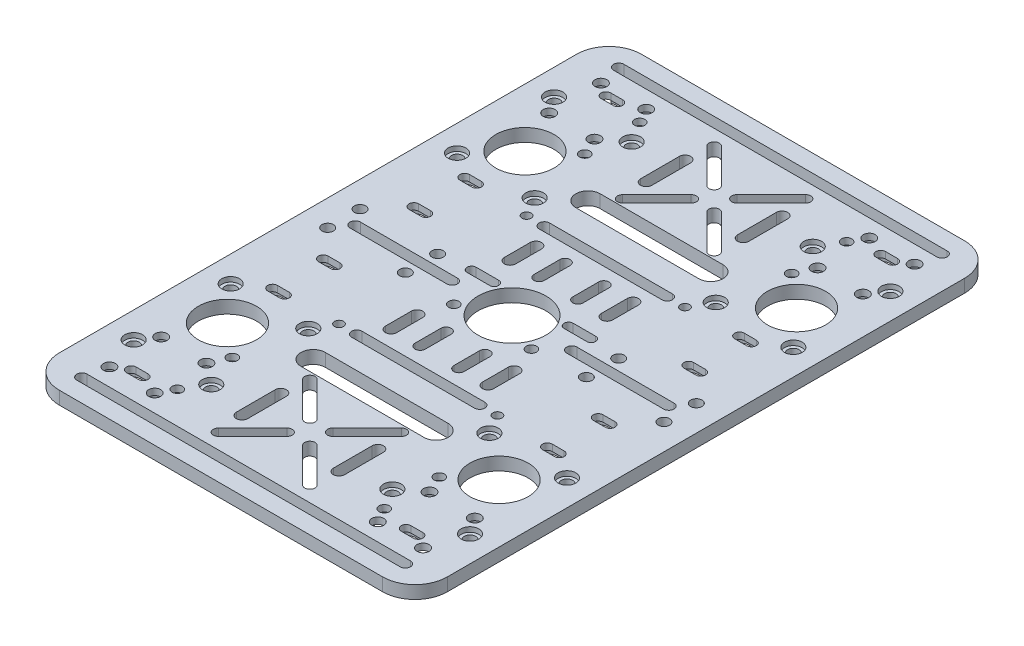
SolidWorks part; units mm, degrees
ref_plane "Front Plane" through (0, 0, 0) normal (0, 0, 1) x (1, 0, 0)
ref_plane "Top Plane" through (0, 0, 0) normal (0, 1, 0) x (1, 0, 0)
ref_plane "Right Plane" through (0, 0, 0) normal (1, 0, 0) x (0, 0, -1)
sketch "Sketch1" plane through (0, 0, 0) normal (0, 1, 0) x (1, 0, 0)
  line L0 (0, 172.909) -> (0, -52.3008) construction
  line L1 (-60, -90) -> (60, -90)
  line L2 (-60, -90) -> (-60, 90)
  line L3 (-60, 90) -> (60, 90)
  line L4 (60, -90) -> (60, 90)
  line L5 (-60, -90) -> (60, 90) construction
  line L6 (-60, 90) -> (60, -90) construction
  line L7 (0, 0) -> (91.3334, 0) construction
  line L8 (-34.5, 171.6818) -> (-34.5, -164.6355) construction
  line L9 (-48.5, 31.1899) -> (-48.5, -305.1274) construction
  line L10 (-15, 68.5) -> (-15, 56.5) construction
  line L13 (-16.75, 68.5) -> (-16.75, 56.5)
  line L16 (-13.25, 68.5) -> (-13.25, 56.5)
  line L19 (15, -68.5) -> (15, -56.5) construction
  line L22 (16.75, -68.5) -> (16.75, -56.5)
  line L25 (13.25, -68.5) -> (13.25, -56.5)
  line L28 (-15, -68.5) -> (-15, -56.5) construction
  line L31 (-16.75, -68.5) -> (-16.75, -56.5)
  line L34 (11.5, 6) -> (18.5, 6) construction
  line L35 (-24.5, -29) -> (24.5, -29) construction
  line L36 (-24.5, -29) -> (-24.5, 29) construction
  line L37 (-24.5, 29) -> (24.5, 29) construction
  line L38 (24.5, -29) -> (24.5, 29) construction
  line L39 (-24.5, -29) -> (24.5, 29) construction
  line L40 (-24.5, 29) -> (24.5, -29) construction
  line L41 (11.5, 7.4) -> (18.5, 7.4)
  line L42 (11.5, 4.6) -> (18.5, 4.6)
  line L43 (-11.5, 6) -> (-18.5, 6) construction
  line L44 (-11.5, 7.4) -> (-18.5, 7.4)
  line L45 (-11.5, 4.6) -> (-18.5, 4.6)
  line L46 (3.5355, 58.9645) -> (14.1421, 48.3579) construction
  line L47 (-17.5, 80) -> (17.5, 80) construction
  line L48 (-17.5, 80) -> (-17.5, 45) construction
  line L49 (-17.5, 45) -> (17.5, 45) construction
  line L50 (17.5, 80) -> (17.5, 45) construction
  line L51 (-17.5, 80) -> (17.5, 45) construction
  line L52 (-17.5, 45) -> (17.5, 80) construction
  line L53 (4.6669, 60.0958) -> (15.2735, 49.4892)
  line L54 (2.4042, 57.8331) -> (13.0108, 47.2265)
  line L55 (-3.5355, 58.9645) -> (-14.1421, 48.3579) construction
  line L56 (-2.4042, 57.8331) -> (-13.0108, 47.2265)
  line L57 (-4.6669, 60.0958) -> (-15.2735, 49.4892)
  line L58 (-3.5355, 66.0355) -> (-14.1421, 76.6421) construction
  line L59 (-4.6669, 64.9042) -> (-15.2735, 75.5108)
  line L60 (-2.4042, 67.1669) -> (-13.0108, 77.7735)
  line L61 (3.5355, 66.0355) -> (14.1421, 76.6421) construction
  line L62 (2.4042, 67.1669) -> (13.0108, 77.7735)
  line L63 (4.6669, 64.9042) -> (15.2735, 75.5108)
  line L64 (3.5355, -58.9645) -> (14.1421, -48.3579) construction
  line L65 (4.6669, -60.0958) -> (15.2735, -49.4892)
  line L66 (2.4042, -57.8331) -> (13.0108, -47.2265)
  line L67 (-3.5355, -58.9645) -> (-14.1421, -48.3579) construction
  line L68 (-2.4042, -57.8331) -> (-13.0108, -47.2265)
  line L69 (-4.6669, -60.0958) -> (-15.2735, -49.4892)
  line L70 (-3.5355, -66.0355) -> (-14.1421, -76.6421) construction
  line L71 (-4.6669, -64.9042) -> (-15.2735, -75.5108)
  line L72 (-2.4042, -67.1669) -> (-13.0108, -77.7735)
  line L73 (3.5355, -66.0355) -> (14.1421, -76.6421) construction
  line L74 (2.4042, -67.1669) -> (13.0108, -77.7735)
  line L75 (4.6669, -64.9042) -> (15.2735, -75.5108)
  line L76 (-19, -42.5) -> (19, -42.5) construction
  line L77 (-29.7, -42.5) -> (29.7, -42.5) construction
  line L79 (-29.7, 42.5) -> (29.7, 42.5) construction
  line L83 (-19, -38.75) -> (19, -38.75)
  line L84 (-19, -46.25) -> (19, -46.25)
  line L85 (-19, 42.5) -> (19, 42.5) construction
  line L86 (-19, 38.75) -> (19, 38.75)
  line L87 (-19, 46.25) -> (19, 46.25)
  line L88 (-48.5, 0) -> (-18.5, 0) construction
  line L97 (-48.5, 1.6) -> (-18.5, 1.6)
  line L98 (-48.5, -1.6) -> (-18.5, -1.6)
  line L99 (-50, -83) -> (50, -83) construction
  line L100 (-50, -81.4) -> (50, -81.4)
  line L101 (-50, -84.6) -> (50, -84.6)
  line L102 (48.5, 0) -> (18.5, 0) construction
  line L103 (48.5, 1.6) -> (18.5, 1.6)
  line L104 (48.5, -1.6) -> (18.5, -1.6)
  line L105 (-50, 83) -> (50, 83) construction
  line L106 (-50, 81.4) -> (50, 81.4)
  line L107 (-50, 84.6) -> (50, 84.6)
  line L108 (15, 68.5) -> (15, 56.5) construction
  line L109 (16.75, 68.5) -> (16.75, 56.5)
  line L110 (13.25, 68.5) -> (13.25, 56.5)
  line L111 (-13.25, -68.5) -> (-13.25, -56.5)
  line L114 (40.65, -29.7) -> (44.35, -29.7) construction
  line L120 (-19, 29) -> (19, 29) construction
  line L121 (-19, 30.6) -> (19, 30.6)
  line L122 (-19, 27.4) -> (19, 27.4)
  line L123 (-6, 22.4) -> (-6, 14.4) construction
  line L124 (-4.4, 22.4) -> (-4.4, 14.4)
  line L125 (-7.6, 22.4) -> (-7.6, 14.4)
  line L126 (-15, 22.4) -> (-15, 14.4) construction
  line L127 (-13.25, 22.4) -> (-13.25, 14.4)
  line L128 (-16.75, 22.4) -> (-16.75, 14.4)
  line L129 (15, 22.4) -> (15, 14.4) construction
  line L130 (13.25, 22.4) -> (13.25, 14.4)
  line L131 (16.75, 22.4) -> (16.75, 14.4)
  line L132 (6, 22.4) -> (6, 14.4) construction
  line L133 (4.4, 22.4) -> (4.4, 14.4)
  line L134 (7.6, 22.4) -> (7.6, 14.4)
  line L135 (15, -22.4) -> (15, -14.4) construction
  line L136 (13.25, -22.4) -> (13.25, -14.4)
  line L137 (16.75, -22.4) -> (16.75, -14.4)
  line L138 (6, -22.4) -> (6, -14.4) construction
  line L139 (4.4, -22.4) -> (4.4, -14.4)
  line L140 (7.6, -22.4) -> (7.6, -14.4)
  line L141 (-6, -22.4) -> (-6, -14.4) construction
  line L142 (-4.4, -22.4) -> (-4.4, -14.4)
  line L143 (-7.6, -22.4) -> (-7.6, -14.4)
  line L144 (-15, -22.4) -> (-15, -14.4) construction
  line L145 (-13.25, -22.4) -> (-13.25, -14.4)
  line L146 (-16.75, -22.4) -> (-16.75, -14.4)
  line L147 (-19, -29) -> (19, -29) construction
  line L148 (-19, -30.6) -> (19, -30.6)
  line L149 (-19, -27.4) -> (19, -27.4)
  line L150 (-42.5, 29.7) -> (42.5, 29.7) construction
  line L151 (-42.5, 29.7) -> (-42.5, -29.7) construction
  line L152 (-42.5, -29.7) -> (42.5, -29.7) construction
  line L153 (42.5, 29.7) -> (42.5, -29.7) construction
  line L154 (-42.5, 29.7) -> (42.5, -29.7) construction
  line L155 (-42.5, -29.7) -> (42.5, 29.7) construction
  line L156 (40.65, -28.2) -> (44.35, -28.2)
  line L157 (40.65, -31.2) -> (44.35, -31.2)
  line L158 (40.65, 29.7) -> (44.35, 29.7) construction
  line L159 (40.65, 28.2) -> (44.35, 28.2)
  line L160 (40.65, 31.2) -> (44.35, 31.2)
  line L161 (-40.65, -29.7) -> (-44.35, -29.7) construction
  line L162 (-40.65, -28.2) -> (-44.35, -28.2)
  line L163 (-40.65, -31.2) -> (-44.35, -31.2)
  line L164 (-40.65, 29.7) -> (-44.35, 29.7) construction
  line L165 (-40.65, 28.2) -> (-44.35, 28.2)
  line L166 (-40.65, 31.2) -> (-44.35, 31.2)
  line L167 (44.35, -14) -> (40.65, -14) construction
  line L168 (44.35, -15.5) -> (40.65, -15.5)
  line L169 (44.35, -12.5) -> (40.65, -12.5)
  line L170 (88.9718, -43.7) -> (45.9541, -43.7) construction
  line L173 (-44.35, -14) -> (-40.65, -14) construction
  line L176 (-44.35, -15.5) -> (-40.65, -15.5)
  line L179 (-44.35, -12.5) -> (-40.65, -12.5)
  line L180 (-44.35, -73.4) -> (-40.65, -73.4) construction
  line L181 (-44.35, -71.9) -> (-40.65, -71.9)
  line L182 (-44.35, -74.9) -> (-40.65, -74.9)
  line L183 (44.35, -73.4) -> (40.65, -73.4) construction
  line L184 (44.35, -71.9) -> (40.65, -71.9)
  line L185 (44.35, -74.9) -> (40.65, -74.9)
  line L186 (44.35, 73.4) -> (40.65, 73.4) construction
  line L187 (44.35, 71.9) -> (40.65, 71.9)
  line L188 (44.35, 74.9) -> (40.65, 74.9)
  line L189 (-44.35, 73.4) -> (-40.65, 73.4) construction
  line L190 (-44.35, 71.9) -> (-40.65, 71.9)
  line L191 (-44.35, 74.9) -> (-40.65, 74.9)
  line L192 (44.35, 14) -> (40.65, 14) construction
  line L193 (44.35, 15.5) -> (40.65, 15.5)
  line L194 (44.35, 12.5) -> (40.65, 12.5)
  line L195 (-44.35, 14) -> (-40.65, 14) construction
  line L196 (-44.35, 15.5) -> (-40.65, 15.5)
  line L197 (-44.35, 12.5) -> (-40.65, 12.5)
  circle A16 centre (-24.5, 29) radius 1.4
  circle A17 centre (24.5, 29) radius 1.4
  circle A18 centre (-24.5, -29) radius 1.4
  circle A19 centre (24.5, -29) radius 1.4
  arc A20 (11.5, 7.4) -> (11.5, 4.6) centre (11.5, 6) ccw
  arc A21 (18.5, 4.6) -> (18.5, 7.4) centre (18.5, 6) ccw
  arc A22 (-11.5, 7.4) -> (-11.5, 4.6) centre (-11.5, 6) cw
  arc A23 (-18.5, 4.6) -> (-18.5, 7.4) centre (-18.5, 6) cw
  circle A24 centre (0, 0) radius 10.5
  arc A25 (4.6669, 60.0958) -> (2.4042, 57.8331) centre (3.5355, 58.9645) ccw
  arc A26 (13.0108, 47.2265) -> (15.2735, 49.4892) centre (14.1421, 48.3579) ccw
  arc A28 (-2.4042, 57.8331) -> (-4.6669, 60.0958) centre (-3.5355, 58.9645) ccw
  arc A29 (-15.2735, 49.4892) -> (-13.0108, 47.2265) centre (-14.1421, 48.3579) ccw
  arc A30 (-4.6669, 64.9042) -> (-2.4042, 67.1669) centre (-3.5355, 66.0355) ccw
  arc A31 (-13.0108, 77.7735) -> (-15.2735, 75.5108) centre (-14.1421, 76.6421) ccw
  arc A32 (2.4042, 67.1669) -> (4.6669, 64.9042) centre (3.5355, 66.0355) ccw
  arc A33 (15.2735, 75.5108) -> (13.0108, 77.7735) centre (14.1421, 76.6421) ccw
  arc A34 (4.6669, -60.0958) -> (2.4042, -57.8331) centre (3.5355, -58.9645) cw
  arc A35 (13.0108, -47.2265) -> (15.2735, -49.4892) centre (14.1421, -48.3579) cw
  arc A36 (-2.4042, -57.8331) -> (-4.6669, -60.0958) centre (-3.5355, -58.9645) cw
  arc A37 (-15.2735, -49.4892) -> (-13.0108, -47.2265) centre (-14.1421, -48.3579) cw
  arc A38 (-4.6669, -64.9042) -> (-2.4042, -67.1669) centre (-3.5355, -66.0355) cw
  arc A39 (-13.0108, -77.7735) -> (-15.2735, -75.5108) centre (-14.1421, -76.6421) cw
  arc A40 (2.4042, -67.1669) -> (4.6669, -64.9042) centre (3.5355, -66.0355) cw
  arc A41 (15.2735, -75.5108) -> (13.0108, -77.7735) centre (14.1421, -76.6421) cw
  circle A42 centre (12, -6) radius 1.6
  circle A43 centre (-12, -6) radius 1.6
  arc A48 (-19, -38.75) -> (-19, -46.25) centre (-19, -42.5) ccw
  arc A49 (19, -46.25) -> (19, -38.75) centre (19, -42.5) ccw
  arc A50 (-19, 38.75) -> (-19, 46.25) centre (-19, 42.5) cw
  arc A51 (19, 46.25) -> (19, 38.75) centre (19, 42.5) cw
  arc A52 (-48.5, 1.6) -> (-48.5, -1.6) centre (-48.5, 0) ccw
  arc A53 (-18.5, -1.6) -> (-18.5, 1.6) centre (-18.5, 0) ccw
  arc A54 (-50, -81.4) -> (-50, -84.6) centre (-50, -83) ccw
  arc A55 (50, -84.6) -> (50, -81.4) centre (50, -83) ccw
  arc A56 (48.5, 1.6) -> (48.5, -1.6) centre (48.5, 0) cw
  arc A57 (18.5, -1.6) -> (18.5, 1.6) centre (18.5, 0) cw
  arc A58 (-50, 81.4) -> (-50, 84.6) centre (-50, 83) cw
  arc A59 (50, 84.6) -> (50, 81.4) centre (50, 83) cw
  arc A60 (16.75, 68.5) -> (13.25, 68.5) centre (15, 68.5) ccw
  arc A61 (13.25, 56.5) -> (16.75, 56.5) centre (15, 56.5) ccw
  arc A68 (-19, 30.6) -> (-19, 27.4) centre (-19, 29) ccw
  arc A69 (19, 27.4) -> (19, 30.6) centre (19, 29) ccw
  arc A70 (-4.4, 22.4) -> (-7.6, 22.4) centre (-6, 22.4) ccw
  arc A71 (-7.6, 14.4) -> (-4.4, 14.4) centre (-6, 14.4) ccw
  arc A72 (-13.25, 22.4) -> (-16.75, 22.4) centre (-15, 22.4) ccw
  arc A73 (-16.75, 14.4) -> (-13.25, 14.4) centre (-15, 14.4) ccw
  arc A74 (13.25, 22.4) -> (16.75, 22.4) centre (15, 22.4) cw
  arc A75 (16.75, 14.4) -> (13.25, 14.4) centre (15, 14.4) cw
  arc A76 (4.4, 22.4) -> (7.6, 22.4) centre (6, 22.4) cw
  arc A77 (7.6, 14.4) -> (4.4, 14.4) centre (6, 14.4) cw
  arc A78 (13.25, -22.4) -> (16.75, -22.4) centre (15, -22.4) ccw
  arc A79 (16.75, -14.4) -> (13.25, -14.4) centre (15, -14.4) ccw
  arc A80 (4.4, -22.4) -> (7.6, -22.4) centre (6, -22.4) ccw
  arc A81 (7.6, -14.4) -> (4.4, -14.4) centre (6, -14.4) ccw
  arc A82 (-4.4, -22.4) -> (-7.6, -22.4) centre (-6, -22.4) cw
  arc A83 (-7.6, -14.4) -> (-4.4, -14.4) centre (-6, -14.4) cw
  arc A84 (-13.25, -22.4) -> (-16.75, -22.4) centre (-15, -22.4) cw
  arc A85 (-16.75, -14.4) -> (-13.25, -14.4) centre (-15, -14.4) cw
  arc A86 (-19, -30.6) -> (-19, -27.4) centre (-19, -29) cw
  arc A87 (19, -27.4) -> (19, -30.6) centre (19, -29) cw
  arc A96 (-16.75, 68.5) -> (-13.25, 68.5) centre (-15, 68.5) cw
  arc A97 (-13.25, 56.5) -> (-16.75, 56.5) centre (-15, 56.5) cw
  arc A98 (16.75, -68.5) -> (13.25, -68.5) centre (15, -68.5) cw
  arc A99 (13.25, -56.5) -> (16.75, -56.5) centre (15, -56.5) cw
  arc A100 (-16.75, -68.5) -> (-13.25, -68.5) centre (-15, -68.5) ccw
  arc A101 (-13.25, -56.5) -> (-16.75, -56.5) centre (-15, -56.5) ccw
  arc A102 (40.65, -28.2) -> (40.65, -31.2) centre (40.65, -29.7) ccw
  arc A103 (44.35, -31.2) -> (44.35, -28.2) centre (44.35, -29.7) ccw
  arc A104 (40.65, 28.2) -> (40.65, 31.2) centre (40.65, 29.7) cw
  arc A105 (44.35, 31.2) -> (44.35, 28.2) centre (44.35, 29.7) cw
  arc A106 (-40.65, -28.2) -> (-40.65, -31.2) centre (-40.65, -29.7) cw
  arc A107 (-44.35, -31.2) -> (-44.35, -28.2) centre (-44.35, -29.7) cw
  arc A108 (-40.65, 28.2) -> (-40.65, 31.2) centre (-40.65, 29.7) ccw
  arc A109 (-44.35, 31.2) -> (-44.35, 28.2) centre (-44.35, 29.7) ccw
  arc A110 (44.35, -15.5) -> (44.35, -12.5) centre (44.35, -14) ccw
  arc A111 (40.65, -12.5) -> (40.65, -15.5) centre (40.65, -14) ccw
  arc A118 (-44.35, -15.5) -> (-44.35, -12.5) centre (-44.35, -14) cw
  arc A119 (-40.65, -12.5) -> (-40.65, -15.5) centre (-40.65, -14) cw
  arc A120 (-44.35, -71.9) -> (-44.35, -74.9) centre (-44.35, -73.4) ccw
  arc A121 (-40.65, -74.9) -> (-40.65, -71.9) centre (-40.65, -73.4) ccw
  arc A122 (44.35, -71.9) -> (44.35, -74.9) centre (44.35, -73.4) cw
  arc A123 (40.65, -74.9) -> (40.65, -71.9) centre (40.65, -73.4) cw
  arc A124 (44.35, 71.9) -> (44.35, 74.9) centre (44.35, 73.4) ccw
  arc A125 (40.65, 74.9) -> (40.65, 71.9) centre (40.65, 73.4) ccw
  arc A126 (-44.35, 71.9) -> (-44.35, 74.9) centre (-44.35, 73.4) cw
  arc A127 (-40.65, 74.9) -> (-40.65, 71.9) centre (-40.65, 73.4) cw
  arc A128 (44.35, 15.5) -> (44.35, 12.5) centre (44.35, 14) cw
  arc A129 (40.65, 12.5) -> (40.65, 15.5) centre (40.65, 14) cw
  arc A130 (-44.35, 15.5) -> (-44.35, 12.5) centre (-44.35, 14) ccw
  arc A131 (-40.65, 12.5) -> (-40.65, 15.5) centre (-40.65, 14) ccw
  point P0 (0, 0)
  point P16 (-15, 62.5)
  point P23 (15, -62.5)
  point P30 (-15, -62.5)
  point P40 (42.5, -29.7)
  point P50 (42.5, -14)
  point P53 (42.5, 29.7)
  point P60 (-42.5, -29.7)
  point P67 (-42.5, 29.7)
  point P70 (0, 0)
  point P81 (15, 6)
  point P88 (-15, 6)
  point P95 (0, 62.5)
  point P100 (8.8388, 53.6612)
  point P110 (-8.8388, 53.6612)
  point P117 (-8.8388, 71.3388)
  point P124 (8.8388, 71.3388)
  point P131 (0, 62.5)
  point P134 (8.8388, -53.6612)
  point P141 (-8.8388, -53.6612)
  point P148 (-8.8388, -71.3388)
  point P155 (8.8388, -71.3388)
  point P171 (0, -42.5)
  point P179 (0, 42.5)
  point P185 (-33.5, 0)
  point P192 (0, -83)
  point P200 (33.5, 0)
  point P207 (0, 83)
  point P213 (15, 62.5)
  point P223 (-42.5, -14)
  point P230 (-42.5, -73.4)
  point P237 (42.5, -73.4)
  point P241 (0, 29)
  point P246 (-6, 18.4)
  point P253 (-15, 18.4)
  point P263 (15, 18.4)
  point P270 (6, 18.4)
  point P277 (15, -18.4)
  point P284 (6, -18.4)
  point P291 (-6, -18.4)
  point P298 (-15, -18.4)
  point P305 (0, -29)
  point P313 (42.5, 73.4)
  point P320 (-42.5, 73.4)
  point P327 (42.5, 14)
  point P334 (-42.5, 14)
  dimension "D11" = 2.8
  dimension "D15" = 21
  dimension "D21" = 15
  dimension "D24" = 3.2
  dimension "D29" = 3
  dimension "D32" = 3.2
  dimension "D39" = 3.2
  dimension "D50" = 14
  dimension "D1" = 120
  dimension "D2" = 180
  dimension "D3" = 14
  dimension "D5" = 34.5
  dimension "D6" = 30
  dimension "D7" = 42.5
  dimension "D8" = 42.5
  dimension "D9" = 49
  dimension "D10" = 58
  dimension "D12" = 7
  dimension "D13" = 2.8
  dimension "D14" = 30
  dimension "D16" = 6
  dimension "D17" = 35
  dimension "D18" = 35
  dimension "D19" = 10
  dimension "D20" = 3.2
  dimension "D22" = 5
  dimension "D25" = 24
  dimension "D26" = 6
  dimension "D27" = 85
  dimension "D28" = 59.4
  dimension "D30" = 38
  dimension "D31" = 7.5
  dimension "D33" = 3.2
  dimension "D34" = 100
  dimension "D35" = 83
  dimension "D36" = 30
  dimension "D37" = 3.5
  dimension "D38" = 12
  dimension "D40" = 38
  dimension "D41" = 8
  dimension "D42" = 3.2
  dimension "D43" = 6
  dimension "D44" = 5
  dimension "D45" = 9
  dimension "D46" = 3.5
  dimension "D47" = 3.7
  dimension "D48" = 3
  dimension "D49" = 3.7
  dimension "D51" = 29.7
  dimension "D23" = 4
extrude "Boss-Extrude1" add sketch "Sketch1" along normal blind 4
sketch "Sketch2" plane through (0, 4, 0) normal (0, 1, 0) x (1, 0, 0)
  line L0 (0, 0) -> (-78.829, 0) construction
  line L1 (-32, -71.5) -> (32, -71.5) construction
  line L2 (-32, -71.5) -> (-32, -54.5) construction
  line L3 (-32, -54.5) -> (32, -54.5) construction
  line L4 (32, -71.5) -> (32, -54.5) construction
  line L5 (-32, -71.5) -> (32, -54.5) construction
  line L6 (-32, -54.5) -> (32, -71.5) construction
  line L7 (0, 0) -> (0, 51.4904) construction
  line L12 (28, 65) -> (52, 65) construction
  line L13 (28, 65) -> (28, 35) construction
  line L14 (28, 35) -> (52, 35) construction
  line L15 (52, 65) -> (52, 35) construction
  line L16 (40, 65) -> (40, 35) construction
  line L17 (52, 50) -> (28, 50) construction
  line L19 (-48.5, 76) -> (-34.5, 76) construction
  line L20 (-48.5, 76) -> (-48.5, 60) construction
  line L21 (-48.5, 60) -> (-34.5, 60) construction
  line L22 (-34.5, 76) -> (-34.5, 60) construction
  line L23 (-48.5, 76) -> (-34.5, 60) construction
  line L24 (-48.5, 60) -> (-34.5, 76) construction
  circle A0 centre (32, -71.5) radius 1.6
  circle A1 centre (32, -54.5) radius 1.6
  circle A2 centre (-32, -71.5) radius 1.6
  circle A3 centre (-32, -54.5) radius 1.6
  circle A4 centre (32, 71.5) radius 1.6
  circle A5 centre (32, 54.5) radius 1.6
  circle A6 centre (-32, 71.5) radius 1.6
  circle A7 centre (-32, 54.5) radius 1.6
  circle A8 centre (52, 35) radius 1.75
  circle A9 centre (28, 35) radius 1.75
  circle A10 centre (28, 65) radius 1.75
  circle A11 centre (52, 65) radius 1.75
  circle A12 centre (-52, 65) radius 1.75
  circle A13 centre (-28, 65) radius 1.75
  circle A14 centre (-28, 35) radius 1.75
  circle A15 centre (-52, 35) radius 1.75
  circle A16 centre (-28, -65) radius 1.75
  circle A17 centre (-52, -65) radius 1.75
  circle A18 centre (-52, -35) radius 1.75
  circle A19 centre (-28, -35) radius 1.75
  circle A20 centre (52, -35) radius 1.75
  circle A21 centre (52, -65) radius 1.75
  circle A22 centre (28, -65) radius 1.75
  circle A23 centre (28, -35) radius 1.75
  circle A24 centre (28, 5) radius 1.75
  circle A25 centre (52, 5) radius 1.75
  circle A26 centre (28, -5) radius 1.75
  circle A27 centre (52, -5) radius 1.75
  circle A28 centre (-52, 5) radius 1.75
  circle A29 centre (-28, 5) radius 1.75
  circle A30 centre (-28, -5) radius 1.75
  circle A31 centre (-52, -5) radius 1.75
  circle A32 centre (-34.5, 76) radius 1.85
  circle A34 centre (-48.5, 76) radius 1.85
  circle A35 centre (-48.5, 60) radius 1.85
  circle A36 centre (-34.5, 60) radius 1.85
  circle A37 centre (34.5, 76) radius 1.85
  circle A38 centre (48.5, 76) radius 1.85
  circle A39 centre (48.5, 60) radius 1.85
  circle A40 centre (34.5, 60) radius 1.85
  circle A41 centre (-34.5, -76) radius 1.85
  circle A42 centre (-48.5, -76) radius 1.85
  circle A43 centre (-48.5, -60) radius 1.85
  circle A44 centre (-34.5, -60) radius 1.85
  circle A45 centre (34.5, -76) radius 1.85
  circle A46 centre (34.5, -60) radius 1.85
  circle A47 centre (48.5, -60) radius 1.85
  circle A48 centre (48.5, -76) radius 1.85
  point P0 (0, -63)
  point P20 (0, -63)
  point P35 (40, 50)
  point P76 (-41.5, 68)
  point P79 (0, 0)
  dimension "D4" = 3.2
  dimension "D5" = 3.2
  dimension "D6" = 3.2
  dimension "D7" = 3.2
  dimension "D10" = 3.5
  dimension "D15" = 3.7
  dimension "D16" = 2
  dimension "D1" = 63
  dimension "D2" = 64
  dimension "D3" = 17
  dimension "D8" = 24
  dimension "D9" = 30
  dimension "D11" = 40
  dimension "D12" = 50
  dimension "D13" = 14
  dimension "D14" = 16
  dimension "D18" = 34.5
  dimension "D19" = 60
  dimension "D17" = 2
extrude "Cut-Extrude1" cut sketch "Sketch2" against normal through all
fillet "Fillet1" radius 10 4 edges at (-60, 2, 90) (60, 2, 90) (60, 2, -90) (-60, 2, -90)
sketch "草图1" plane through (0, 4, 0) normal (0, 1, 0) x (1, 0, 0)
  line L0 (0, 0) -> (94.0983, 0) construction
  line L1 (0, 0) -> (0, 105.2268) construction
  circle A0 centre (-52, 65) radius 1.75 construction
  circle A1 centre (-52, 65) radius 1.75 construction
  circle A2 centre (-28, 65) radius 1.75 construction
  circle A3 centre (-28, 65) radius 1.75 construction
  circle A4 centre (-28, 65) radius 2.75
  circle A5 centre (-52, 65) radius 2.75
  circle A6 centre (52, 65) radius 2.75
  circle A7 centre (28, 65) radius 2.75
  circle A8 centre (-52, -65) radius 2.75
  circle A9 centre (-28, -65) radius 2.75
  circle A10 centre (28, -65) radius 2.75
  circle A11 centre (52, -65) radius 2.75
  circle A12 centre (52, 35) radius 1.75 construction
  circle A13 centre (52, 35) radius 1.75 construction
  circle A14 centre (28, 35) radius 1.75 construction
  circle A15 centre (28, 35) radius 1.75 construction
  circle A16 centre (52, 35) radius 2.75
  circle A17 centre (28, 35) radius 2.75
  circle A18 centre (-28, 35) radius 2.75
  circle A19 centre (-52, 35) radius 2.75
  circle A20 centre (52, -35) radius 2.75
  circle A21 centre (28, -35) radius 2.75
  circle A22 centre (-52, -35) radius 2.75
  circle A23 centre (-28, -35) radius 2.75
  point P45 (0, 0)
  dimension "D1" = 5.5
  dimension "D2" = 5.5
  dimension "D3" = 5.5
  dimension "D4" = 5.5
extrude "切除-拉伸1" cut sketch "草图1" against normal blind 1.5
sketch "草图2" plane through (0, 0, 0) normal (0, -1, 0) x (1, 0, 0)
  line L0 (40.65, 74.9) -> (44.35, 74.9) construction
  line L1 (44.35, 71.9) -> (40.65, 71.9) construction
  line L2 (40.65, 74.9) -> (44.35, 74.9) construction
  line L3 (44.35, 71.9) -> (40.65, 71.9) construction
  line L4 (40.65, 31.2) -> (44.35, 31.2) construction
  line L5 (44.35, 28.2) -> (40.65, 28.2) construction
  line L6 (40.65, 31.2) -> (44.35, 31.2) construction
  line L7 (44.35, 28.2) -> (40.65, 28.2) construction
  line L8 (87.1899, 0) -> (61.1341, 0) construction
  line L9 (0, 12.4924) -> (0, 16.3383) construction
  line L10 (40.65, 15.5) -> (44.35, 15.5) construction
  line L11 (44.35, 12.5) -> (40.65, 12.5) construction
  line L12 (40.65, 15.5) -> (44.35, 15.5) construction
  line L13 (44.35, 12.5) -> (40.65, 12.5) construction
  line L14 (44.35, 73.4) -> (40.65, 73.4) construction
  line L15 (44.35, 70.4) -> (40.65, 70.4)
  line L16 (44.35, 76.4) -> (40.65, 76.4)
  line L17 (40.65, 29.7) -> (44.35, 29.7) construction
  line L18 (40.65, 32.7) -> (44.35, 32.7)
  line L19 (40.65, 26.7) -> (44.35, 26.7)
  line L20 (44.35, 14) -> (40.65, 14) construction
  line L21 (44.35, 11) -> (40.65, 11)
  line L22 (44.35, 17) -> (40.65, 17)
  line L23 (40.65, -29.7) -> (44.35, -29.7) construction
  line L24 (40.65, -32.7) -> (44.35, -32.7)
  line L25 (40.65, -26.7) -> (44.35, -26.7)
  line L26 (44.35, -14) -> (40.65, -14) construction
  line L27 (44.35, -11) -> (40.65, -11)
  line L28 (44.35, -17) -> (40.65, -17)
  line L29 (44.35, -73.4) -> (40.65, -73.4) construction
  line L30 (44.35, -70.4) -> (40.65, -70.4)
  line L31 (44.35, -76.4) -> (40.65, -76.4)
  line L32 (-44.35, -73.4) -> (-40.65, -73.4) construction
  line L33 (-44.35, -70.4) -> (-40.65, -70.4)
  line L34 (-44.35, -76.4) -> (-40.65, -76.4)
  line L35 (-40.65, -29.7) -> (-44.35, -29.7) construction
  line L36 (-40.65, -32.7) -> (-44.35, -32.7)
  line L37 (-40.65, -26.7) -> (-44.35, -26.7)
  line L38 (-44.35, -14) -> (-40.65, -14) construction
  line L39 (-44.35, -11) -> (-40.65, -11)
  line L40 (-44.35, -17) -> (-40.65, -17)
  line L41 (-44.35, 14) -> (-40.65, 14) construction
  line L42 (-44.35, 11) -> (-40.65, 11)
  line L43 (-44.35, 17) -> (-40.65, 17)
  line L44 (-40.65, 29.7) -> (-44.35, 29.7) construction
  line L45 (-40.65, 32.7) -> (-44.35, 32.7)
  line L46 (-40.65, 26.7) -> (-44.35, 26.7)
  line L47 (-44.35, 73.4) -> (-40.65, 73.4) construction
  line L48 (-44.35, 70.4) -> (-40.65, 70.4)
  line L49 (-44.35, 76.4) -> (-40.65, 76.4)
  arc A0 (44.35, 71.9) -> (44.35, 74.9) centre (44.35, 73.4) ccw construction
  arc A1 (40.65, 74.9) -> (40.65, 71.9) centre (40.65, 73.4) ccw construction
  arc A2 (44.35, 71.9) -> (44.35, 74.9) centre (44.35, 73.4) ccw construction
  arc A3 (40.65, 74.9) -> (40.65, 71.9) centre (40.65, 73.4) ccw construction
  arc A4 (44.35, 28.2) -> (44.35, 31.2) centre (44.35, 29.7) ccw construction
  arc A5 (44.35, 28.2) -> (44.35, 31.2) centre (44.35, 29.7) ccw construction
  arc A6 (40.65, 31.2) -> (40.65, 28.2) centre (40.65, 29.7) ccw construction
  arc A7 (40.65, 31.2) -> (40.65, 28.2) centre (40.65, 29.7) ccw construction
  arc A8 (40.65, 15.5) -> (40.65, 12.5) centre (40.65, 14) ccw construction
  arc A9 (44.35, 12.5) -> (44.35, 15.5) centre (44.35, 14) ccw construction
  arc A10 (40.65, 15.5) -> (40.65, 12.5) centre (40.65, 14) ccw construction
  arc A11 (44.35, 12.5) -> (44.35, 15.5) centre (44.35, 14) ccw construction
  arc A12 (44.35, 70.4) -> (44.35, 76.4) centre (44.35, 73.4) ccw
  arc A13 (40.65, 76.4) -> (40.65, 70.4) centre (40.65, 73.4) ccw
  arc A14 (40.65, 32.7) -> (40.65, 26.7) centre (40.65, 29.7) ccw
  arc A15 (44.35, 26.7) -> (44.35, 32.7) centre (44.35, 29.7) ccw
  arc A16 (44.35, 11) -> (44.35, 17) centre (44.35, 14) ccw
  arc A17 (40.65, 17) -> (40.65, 11) centre (40.65, 14) ccw
  circle A18 centre (-34.5, 60) radius 1.85 construction
  circle A19 centre (-34.5, 60) radius 1.85 construction
  circle A20 centre (-48.5, 60) radius 1.85 construction
  circle A21 centre (-48.5, 60) radius 1.85 construction
  circle A22 centre (-48.5, 76) radius 1.85 construction
  circle A23 centre (-48.5, 76) radius 1.85 construction
  circle A24 centre (-34.5, 76) radius 1.85 construction
  circle A25 centre (-34.5, 76) radius 1.85 construction
  circle A26 centre (-48.5, 60) radius 3
  circle A27 centre (-34.5, 60) radius 3
  circle A28 centre (-48.5, 76) radius 3
  circle A29 centre (-34.5, 76) radius 3
  arc A30 (40.65, -32.7) -> (40.65, -26.7) centre (40.65, -29.7) cw
  arc A31 (44.35, -26.7) -> (44.35, -32.7) centre (44.35, -29.7) cw
  arc A32 (44.35, -11) -> (44.35, -17) centre (44.35, -14) cw
  arc A33 (40.65, -17) -> (40.65, -11) centre (40.65, -14) cw
  arc A34 (44.35, -70.4) -> (44.35, -76.4) centre (44.35, -73.4) cw
  arc A35 (40.65, -76.4) -> (40.65, -70.4) centre (40.65, -73.4) cw
  arc A36 (-44.35, -70.4) -> (-44.35, -76.4) centre (-44.35, -73.4) ccw
  arc A37 (-40.65, -76.4) -> (-40.65, -70.4) centre (-40.65, -73.4) ccw
  arc A38 (-40.65, -32.7) -> (-40.65, -26.7) centre (-40.65, -29.7) ccw
  arc A39 (-44.35, -26.7) -> (-44.35, -32.7) centre (-44.35, -29.7) ccw
  arc A40 (-44.35, -11) -> (-44.35, -17) centre (-44.35, -14) ccw
  arc A41 (-40.65, -17) -> (-40.65, -11) centre (-40.65, -14) ccw
  arc A42 (-44.35, 11) -> (-44.35, 17) centre (-44.35, 14) cw
  arc A43 (-40.65, 17) -> (-40.65, 11) centre (-40.65, 14) cw
  arc A44 (-40.65, 32.7) -> (-40.65, 26.7) centre (-40.65, 29.7) cw
  arc A45 (-44.35, 26.7) -> (-44.35, 32.7) centre (-44.35, 29.7) cw
  arc A46 (-44.35, 70.4) -> (-44.35, 76.4) centre (-44.35, 73.4) cw
  arc A47 (-40.65, 76.4) -> (-40.65, 70.4) centre (-40.65, 73.4) cw
  circle A48 centre (48.5, 76) radius 3
  circle A49 centre (34.5, 76) radius 3
  circle A50 centre (34.5, 60) radius 3
  circle A51 centre (48.5, 60) radius 3
  circle A52 centre (34.5, -60) radius 3
  circle A53 centre (48.5, -60) radius 3
  circle A54 centre (48.5, -76) radius 3
  circle A55 centre (34.5, -76) radius 3
  circle A56 centre (-34.5, -76) radius 3
  circle A57 centre (-48.5, -76) radius 3
  circle A58 centre (-48.5, -60) radius 3
  circle A59 centre (-34.5, -60) radius 3
  circle A60 centre (-32, 71.5) radius 1.6 construction
  circle A61 centre (-32, 71.5) radius 1.6
  circle A62 centre (-32, 54.5) radius 1.6 construction
  circle A63 centre (-32, 54.5) radius 1.6
  circle A64 centre (-32, 54.5) radius 3
  circle A65 centre (-32, 71.5) radius 3
  circle A66 centre (32, 71.5) radius 3
  circle A67 centre (32, 54.5) radius 3
  circle A68 centre (32, -71.5) radius 3
  circle A69 centre (32, -54.5) radius 3
  circle A70 centre (-32, -54.5) radius 3
  circle A71 centre (-32, -71.5) radius 3
  point P20 (42.5, 73.4)
  point P28 (42.5, 29.7)
  point P33 (42.5, 14)
  point P56 (42.5, -29.7)
  point P63 (42.5, -14)
  point P70 (42.5, -73.4)
  point P78 (-42.5, -73.4)
  point P85 (-42.5, -29.7)
  point P92 (-42.5, -14)
  point P99 (-42.5, 14)
  point P106 (-42.5, 29.7)
  point P113 (-42.5, 73.4)
  dimension "D4" = 6
  dimension "D5" = 6
  dimension "D6" = 6
  dimension "D7" = 6
  dimension "D8" = 6
  dimension "D9" = 6
  dimension "D1" = 6
  dimension "D2" = 6
  dimension "D3" = 6
extrude "切除-拉伸2" cut sketch "草图2" against normal blind 2 contours A52 | A26 | A28 | A47 L48 A46 L49 | A29 | A27 | A49 | A50 | A51 | A48 | L16 A13 L15 A12 | A14 L19 A15 L18 | A17 L21 A16 L22 | L43 A43 L42 A42 | A44 L46 A45 L45 | A41 L39 A40 L40 | A38 L37 A39 L36 | A32 L28 A33 L27 | A31 L24 A30 L25 | A53 | A54 | A35 L30 A34 L31 | A55 | A56 | A57 | L34 A37 L33 A36 | A58 | A59 | A65 | A64 | A67 | A66 | A70 | A71 | A69 | A68
sketch "草图3" plane through (0, 4, 0) normal (0, 1, 0) x (1, 0, 0)
  line L0 (82.2994, 0) -> (124.5382, 0) construction
  line L1 (0, -53.0448) -> (0, 38.6094) construction
  circle A0 centre (42, -46) radius 9
  circle A1 centre (-42, -46) radius 9
  circle A2 centre (-42, 46) radius 9
  circle A3 centre (42, 46) radius 9
  dimension "D3" = 18
  dimension "D1" = 46
  dimension "D2" = 42
extrude "切除-拉伸3" cut sketch "草图3" against normal through all
